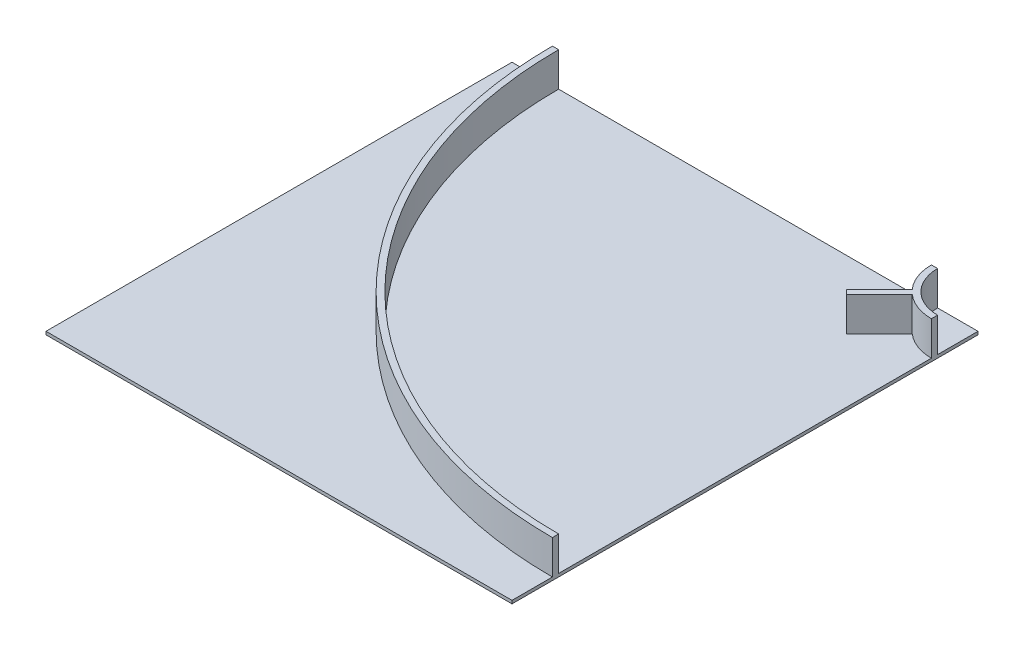
SolidWorks part; units mm, degrees
ref_plane "Front Plane" through (0, 0, 0) normal (0, 0, 1) x (1, 0, 0)
ref_plane "Top Plane" through (0, 0, 0) normal (0, 1, 0) x (1, 0, 0)
ref_plane "Right Plane" through (0, 0, 0) normal (1, 0, 0) x (0, 0, -1)
sketch "Sketch2" plane through (0, 0, 0) normal (0, 1, 0) x (1, 0, 0)
  line L1 (-750, 750) -> (750, 750)
  line L2 (-750, 750) -> (-750, -750)
  line L3 (-750, -750) -> (750, -750)
  line L4 (750, 750) -> (750, -750)
  line L5 (-750, 750) -> (750, -750) construction
  line L6 (-750, -750) -> (750, 750) construction
  point P0 (0, 0)
  dimension "D1" = 1500
  dimension "D2" = 1500
extrude "Boss-Extrude1" add sketch "Sketch2" along normal blind 10
sketch "Sketch3" plane through (0, 10, 0) normal (0, 1, 0) x (1, 0, 0)
  line L0 (620, 750) -> (620, -750) construction
  line L1 (750, 750) -> (-750, 750) construction
  line L2 (-750, -750) -> (750, -750) construction
  line L3 (600, 750) -> (600, -750) construction
  line L4 (750, -750) -> (750, 750) construction
  line L5 (-750, -600) -> (750, -600) construction
  line L6 (-750, 750) -> (-750, -750) construction
  line L7 (-750, -620) -> (750, -620) construction
  line L8 (-750, 0) -> (750, 0) construction
  line L9 (0, 750) -> (0, -750) construction
  line L10 (-750, 620) -> (750, 620) construction
  line L11 (-750, 600) -> (750, 600) construction
  line L12 (-620, 750) -> (-620, -750) construction
  line L13 (-600, 750) -> (-600, -750) construction
  circle A0 centre (750, 750) radius 150
  circle A1 centre (750, 750) radius 1350
  circle A2 centre (750, 750) radius 130
  circle A3 centre (750, 750) radius 1370
  line M3 (750, -750) -> (750, 750)
  line M4 (750, 750) -> (-750, 750)
  dimension "D6" = 150
  dimension "D5" = 20
  dimension "D7" = 20
  dimension "D8" = 150
extrude "Boss-Extrude2" add sketch "Sketch3" along normal blind 110 contours A3 A1 M4 M3 | A2 A0 M4 M3
sketch "Sketch4" plane through (0, 10, 0) normal (0, 1, 0) x (1, 0, 0)
  line L0 (750, 750) -> (-750, -750) construction
  line L1 (545.175, 531.0329) -> (651.241, 637.0989)
  line L2 (545.175, 531.0329) -> (531.0329, 545.175)
  line L3 (651.241, 637.0989) -> (637.0989, 651.241)
  line L4 (531.0329, 545.175) -> (637.0989, 651.241)
  line L5 (545.175, 531.0329) -> (637.0989, 651.241) construction
  line L6 (651.241, 637.0989) -> (531.0329, 545.175) construction
  line L7 (644.1699, 644.1699) -> (538.1039, 538.1039) construction
  arc A5 (600, 750) -> (750, 600) centre (750, 750) ccw construction
  point P5 (591.1369, 591.1369)
  dimension "D1" = 20
extrude "Boss-Extrude3" add sketch "Sketch4" along normal up to surface (110 mm away) up to face at (665.5025, 120, -665.5025)
equation "\"CellSize\"=1500"
equation "\"D1@Sketch2\"=\"CellSize\""
equation "\"D2@Sketch2\"=\"CellSize\""
equation "\"TrackWidth\"= 1200"
equation "\"C\"=342.079"
equation "\"WallWidth\"=20"
equation "\"D6@Sketch3\"=\"EdgeWidth\""
equation "\"D5@Sketch3\"=\"WallWidth\""
equation "\"D7@Sketch3\"=\"WallWidth\""
equation "\"EdgeWidth\"= ( \"CellSize\" - \"TrackWidth\" ) / 2"
equation "\"D8@Sketch3\"=\"EdgeWidth\""
equation "\"D1@Sketch4\"=\"WallWidth\""
